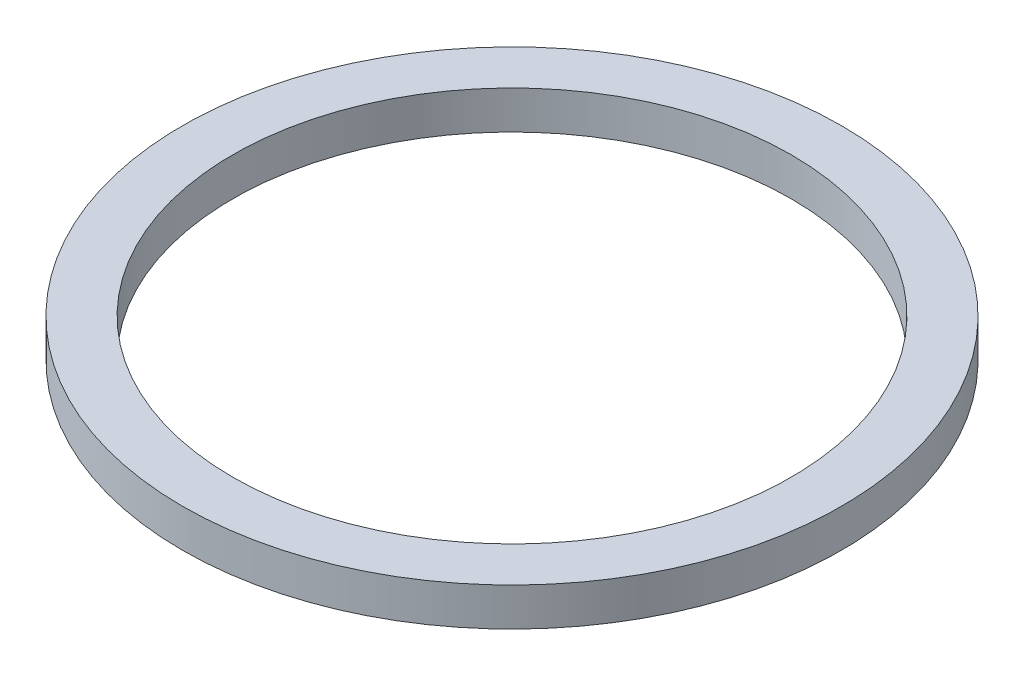
SolidWorks part; units mm, degrees
ref_plane "Front Plane" through (0, 0, 0) normal (0, 0, 1) x (1, 0, 0)
ref_plane "Top Plane" through (0, 0, 0) normal (0, 1, 0) x (1, 0, 0)
ref_plane "Right Plane" through (0, 0, 0) normal (1, 0, 0) x (0, 0, -1)
sketch "Sketch1" plane through (0, 0, 0) normal (0, 1, 0) x (1, 0, 0)
  circle A0 centre (0, 0) radius 9.5
  dimension "D1" = 19
extrude "Boss-Extrude1" add sketch "Sketch1" along normal blind 1.1
sketch "Sketch2" plane through (0, 1.1, 0) normal (0, 1, 0) x (1, 0, 0)
  circle A0 centre (0, 0) radius 8.05
  dimension "D1" = 16.1
extrude "Cut-Extrude1" cut sketch "Sketch2" against normal through all
